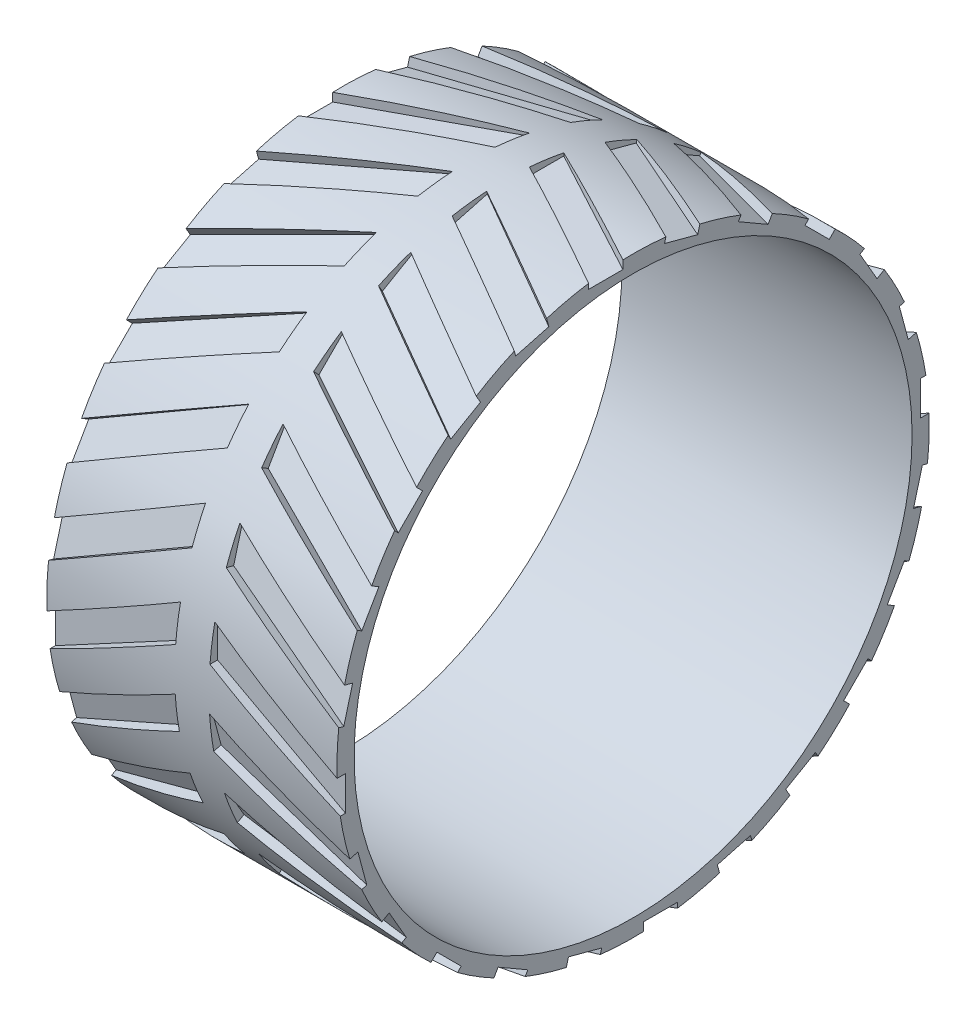
SolidWorks part; units mm, degrees
material "Silicon Rubber"
ref_plane "Front Plane" through (0, 0, 0) normal (0, 0, 1) x (1, 0, 0)
ref_plane "Top Plane" through (0, 0, 0) normal (0, 1, 0) x (1, 0, 0)
ref_plane "Right Plane" through (0, 0, 0) normal (1, 0, 0) x (0, 0, -1)
sketch "Sketch1" plane through (0, 0, 0) normal (1, 0, 0) x (0, 0, -1)
  circle A0 centre (0, 0) radius 32.5
  circle A1 centre (0, 0) radius 34.5
  dimension "D1" = 65
  dimension "D2" = 69
extrude "Boss-Extrude1" add sketch "Sketch1" along normal blind 33.8
ref_plane "Plane1" through (0, 33.5, 0) normal (0, 1, 0) x (1, 0, 0)
sketch "Sketch2" plane through (0, 33.5, 0) normal (0, 1, 0) x (1, 0, 0)
  line L0 (0, 0) -> (33.8, 0) construction
  line L1 (33.8, -34.5) -> (33.8, 34.5) construction
  line L2 (16.9, 49.2036) -> (16.9, -49.2036) construction
  line L3 (0, -1.1846) -> (16.9, 7.9004)
  line L4 (0, 34.5) -> (0, -34.5) construction
  line L5 (0, -1.1846) -> (0, -5.1846)
  line L6 (0, -5.1846) -> (16.9, 3.9004)
  line L7 (16.9, 7.9004) -> (16.9, 3.9004)
  line L8 (33.8, -1.1846) -> (33.8, -5.1846)
  line L9 (33.8, -5.1846) -> (16.9, 3.9004)
  line L10 (33.8, -1.1846) -> (16.9, 7.9004)
  point P8 (16.9, 0)
  dimension "D1" = 4
  dimension "D2" = 4
extrude "Cut-Extrude1" cut sketch "Sketch2" along normal blind 30.8 contours L7 L3 L5 L6 | L8 L10 L7 L9
pattern_circular "CirPattern2" count 24 every 15 about axis through (0, 0, 0) along (1, 0, 0) of "Cut-Extrude1"
ref_plane "Plane2" through (16.9, 0, 0) normal (-1, 0, 0) x (0, 0, 1)
sketch "Sketch4" plane through (16.9, 0, 0) normal (-1, 0, 0) x (0, 0, 1)
  circle A0 centre (0, 0) radius 32.5
  circle A1 centre (0, 0) radius 34.5
extrude "Boss-Extrude2" add sketch "Sketch4" along normal blind 2 and the other way blind 2
